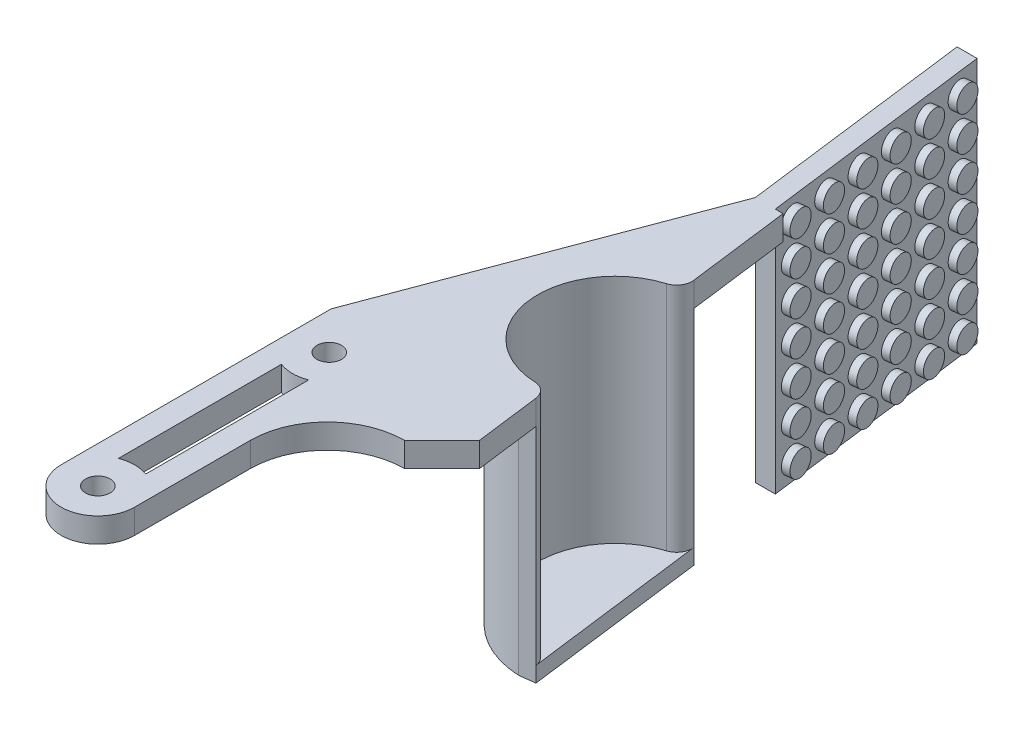
SolidWorks part; units mm, degrees
ref_plane "Alzado" through (0, 0, 0) normal (0, 0, 1) x (1, 0, 0)
ref_plane "Planta" through (0, 0, 0) normal (0, 1, 0) x (1, 0, 0)
ref_plane "Vista lateral" through (0, 0, 0) normal (1, 0, 0) x (0, 0, -1)
sketch "Croquis1" plane through (0, 0, 0) normal (0, 1, 0) x (1, 0, 0)
  line L0 (-12.5, 40) -> (12.5, -40) construction
  line L1 (-12.5, 40) -> (12.5, 40) construction
  line L2 (-12.5, 40) -> (-12.5, -40) construction
  line L3 (-12.5, -40) -> (12.5, -40) construction
  line L4 (12.5, 40) -> (12.5, -40) construction
  line L5 (-12.5, 0) -> (-12.5, -40)
  line L6 (-12.5, -40) -> (-2.975, -40)
  line L7 (-2.975, -40) -> (-2.975, -20)
  line L8 (7.025, -10) -> (12.5, -10)
  line L9 (12.5, -10) -> (12.5, 40)
  line L10 (12.5, 40) -> (2.5, 40)
  line L11 (2.5, 40) -> (-12.5, 0)
  circle A0 centre (-7.7375, -5) radius 1.5875
  circle A1 centre (-7.7375, -35) radius 1.5875
  arc A2 (-2.975, -20) -> (7.025, -10) centre (7.025, -20) cw
  dimension "D5" = 3.175
  dimension "D6" = 3.175
  dimension "D12" = 10
  dimension "D1" = 25
  dimension "D2" = 80
  dimension "D3" = 9.525
  dimension "D4" = 30
  dimension "D7" = 4.7625
  dimension "D8" = 5
  dimension "D9" = 10
  dimension "D10" = 40
  dimension "D11" = 50
extrude "Saliente-Extruir1" add sketch "Croquis1" along normal blind 3.175
sketch "Croquis2" plane through (0, 3.175, 0) normal (0, 1, 0) x (1, 0, 0)
  line L0 (12.5, -10) -> (6.1, 40)
  line L1 (12.5, 40) -> (2.5, 40) construction
  line L2 (6.1, 40) -> (12.5, 40)
  line L3 (12.5, 40) -> (12.5, -10)
  dimension "D1" = 6.4
extrude "Cortar-Extruir1" cut sketch "Croquis2" against normal blind 3.175
sketch "Croquis3" plane through (0, 3.175, 0) normal (0, 1, 0) x (1, 0, 0)
  line L1 (-2.975, -40) -> (-2.975, -20) construction
  line L2 (-12.5, -35) -> (-12.5, -40)
  line L3 (-12.5, -40) -> (-2.975, -40)
  line L4 (-2.975, -40) -> (-2.975, -35)
  line L5 (-9.5, -9.4271) -> (-9.5, -30.5756)
  line L6 (-5.975, -14.8038) -> (-5.975, -30.5756)
  line L7 (-12.5, 0) -> (-12.5, -40) construction
  line L8 (-5.975, -14.8038) -> (-5.975, -9.4271)
  line L22 (7.025, -6) -> (7.9554, -6)
  line L23 (7.9554, -6) -> (3.2646, 30.6468)
  line L24 (3.2646, 30.6468) -> (-8.5, -0.7253)
  line L25 (-8.5, -0.7253) -> (-8.5, -36)
  line L26 (-8.5, -36) -> (-6.975, -36)
  line L27 (-6.975, -36) -> (-6.975, -20)
  line L28 (7.025, -6) -> (7.9554, -6)
  arc A2 (-9.5, -9.4271) -> (-5.975, -9.4271) centre (-7.7375, -5) ccw
  arc A3 (-12.5, -35) -> (-2.975, -35) centre (-7.7375, -35) ccw
  arc A4 (-5.975, -30.5756) -> (-9.5, -30.5756) centre (-7.7375, -35) ccw
  arc A6 (7.025, -6) -> (-6.975, -20) centre (7.025, -20) ccw
  dimension "D1" = 9.53
  dimension "D2" = 3
  dimension "D3" = 3
  dimension "D5" = 4
extrude "Cortar-Extruir3" cut sketch "Croquis3" against normal blind 10 contours A4 L6 L8 A2 L5 | A3 L4 L3 L2
sketch "Croquis5" plane through (0, 3.175, 0) normal (0, 1, 0) x (1, 0, 0)
  line L0 (6.1, 40) -> (12.5, -10) construction
  line L1 (7.025, -10) -> (11.8787, -5.1463)
  line L2 (11.8787, -5.1463) -> (12.5, -10)
  line L3 (12.5, -10) -> (7.025, -10)
  circle A0 centre (9.3, 15) radius 10
  dimension "D1" = 20
  dimension "D2" = 25
  dimension "D3" = 45
extrude "Cortar-Extruir8" cut sketch "Croquis5" against normal blind 10
fillet "Redondeo2" radius 2 2 edges at (8.0304, 1.5875, -24.9191) (10.5696, 1.5875, -5.0809)
sketch "Sketch1" plane through (0, 3.175, 0) normal (0, 1, 0) x (1, 0, 0)
  line L0 (5.8139, 26.4825) -> (7.7977, 26.7364)
  line L2 (8.8184, 3.0097) -> (10.8023, 3.2636)
  arc A0 (6.3949, 24.5687) -> (8.8987, 5.0081) centre (9.3, 15) ccw construction
  arc A1 (6.3949, 24.5687) -> (8.8987, 5.0081) centre (9.3, 15) ccw
  arc A2 (6.3949, 24.5687) -> (7.7977, 26.7364) centre (5.8139, 26.4825) ccw construction
  arc A3 (6.3949, 24.5687) -> (7.7977, 26.7364) centre (5.8139, 26.4825) ccw
  arc A4 (10.8023, 3.2636) -> (8.8987, 5.0081) centre (8.8184, 3.0097) ccw construction
  arc A5 (10.8023, 3.2636) -> (8.8987, 5.0081) centre (8.8184, 3.0097) ccw
  arc A6 (5.8139, 26.4825) -> (5.8139, 26.4825) centre (5.8139, 26.4825) cw
  arc A7 (5.8139, 26.4825) -> (8.8184, 3.0097) centre (9.3, 15) ccw
  arc A8 (8.8184, 3.0097) -> (8.8184, 3.0097) centre (8.8184, 3.0097) cw
  dimension "D1" = 2
extrude "Boss-Extrude1" add sketch "Sketch1" against normal blind 30
sketch "Sketch2" plane through (0, -26.825, 0) normal (0, -1, 0) x (1, 0, 0)
  line L0 (10.8023, -3.2636) -> (7.7977, -26.7364)
  line L2 (5.8139, -26.4825) -> (7.7977, -26.7364)
  line L3 (10.8023, -3.2636) -> (8.8184, -3.0097)
  line L4 (5.8139, -26.4825) -> (7.7977, -26.7364)
  line L5 (10.8023, -3.2636) -> (8.8184, -3.0097)
  arc A4 (7.7977, -26.7364) -> (6.3949, -24.5687) centre (5.8139, -26.4825) ccw
  arc A5 (8.8987, -5.0081) -> (6.3949, -24.5687) centre (9.3, -15) ccw
  arc A6 (8.8987, -5.0081) -> (10.8023, -3.2636) centre (8.8184, -3.0097) ccw
  arc A7 (8.8184, -3.0097) -> (5.8139, -26.4825) centre (9.3, -15) ccw
  arc A11 (8.8184, -3.0097) -> (5.8139, -26.4825) centre (9.3, -15) ccw
  dimension "D1" = 0
extrude "Boss-Extrude2" add sketch "Sketch2" along normal blind 2
sketch "Sketch3" plane through (0, 3.175, 0) normal (0, 1, 0) x (1, 0, 0)
  line L0 (1.2518, 70) -> (-1.34, 70)
  line L1 (2.5, 40) -> (-1.34, 70)
  line L2 (6.1, 40) -> (7.7977, 26.7364) construction
  line L4 (5.0918, 40) -> (5.3981, 37.6073) construction
  line L7 (6.1, 40) -> (2.5, 40) construction
  line L8 (5.0918, 40) -> (2.5, 40)
  line L9 (5.0918, 40) -> (1.2518, 70)
  dimension "D1" = 30
  dimension "D2" = 1
extrude "Boss-Extrude3" add sketch "Sketch3" against normal up to surface (32 mm away) up to face at (5.8283, -28.825, -14.5556)
sketch "Sketch6" plane through (10.0472, 0, -1.286) normal (0.9919, 0, -0.127) x (-0.127, 0, -0.9919)
  line L2 (39.0298, -28.825) -> (69.2746, -28.825) construction
  line L3 (39.0298, -28.825) -> (39.0298, 0) construction
  circle A0 centre (41.5298, -26.325) radius 1.59
  circle A1 centre (46.5298, -26.325) radius 1.59
  circle A2 centre (51.5298, -26.325) radius 1.59
  circle A3 centre (56.5298, -26.325) radius 1.59
  circle A4 centre (61.5298, -26.325) radius 1.59
  circle A5 centre (66.5298, -26.325) radius 1.59
  circle A6 centre (46.5298, -21.825) radius 1.59
  circle A7 centre (51.5298, -21.825) radius 1.59
  circle A8 centre (56.5298, -21.825) radius 1.59
  circle A9 centre (61.5298, -21.825) radius 1.59
  circle A10 centre (66.5298, -21.825) radius 1.59
  circle A11 centre (46.5298, -17.325) radius 1.59
  circle A12 centre (51.5298, -17.325) radius 1.59
  circle A13 centre (56.5298, -17.325) radius 1.59
  circle A14 centre (61.5298, -17.325) radius 1.59
  circle A15 centre (66.5298, -17.325) radius 1.59
  circle A16 centre (46.5298, -12.825) radius 1.59
  circle A17 centre (51.5298, -12.825) radius 1.59
  circle A18 centre (56.5298, -12.825) radius 1.59
  circle A19 centre (61.5298, -12.825) radius 1.59
  circle A20 centre (66.5298, -12.825) radius 1.59
  circle A21 centre (46.5298, -8.325) radius 1.59
  circle A22 centre (51.5298, -8.325) radius 1.59
  circle A23 centre (56.5298, -8.325) radius 1.59
  circle A24 centre (61.5298, -8.325) radius 1.59
  circle A25 centre (66.5298, -8.325) radius 1.59
  circle A26 centre (46.5298, -3.825) radius 1.59
  circle A27 centre (51.5298, -3.825) radius 1.59
  circle A28 centre (56.5298, -3.825) radius 1.59
  circle A29 centre (61.5298, -3.825) radius 1.59
  circle A30 centre (66.5298, -3.825) radius 1.59
  circle A31 centre (46.5298, 0.675) radius 1.59
  circle A32 centre (51.5298, 0.675) radius 1.59
  circle A33 centre (56.5298, 0.675) radius 1.59
  circle A34 centre (61.5298, 0.675) radius 1.59
  circle A35 centre (66.5298, 0.675) radius 1.59
  circle A36 centre (41.5298, -21.825) radius 1.59
  circle A37 centre (41.5298, -17.325) radius 1.59
  circle A38 centre (41.5298, -12.825) radius 1.59
  circle A39 centre (41.5298, -8.325) radius 1.59
  circle A40 centre (41.5298, -3.825) radius 1.59
  circle A41 centre (41.5298, 0.675) radius 1.59
  dimension "D1" = 3.18
  dimension "D2" = 2.5
  dimension "D3" = 2.5
  dimension "D4" = 6
  dimension "D5" = 7
extrude "Boss-Extrude5" add sketch "Sketch6" along normal blind 1
